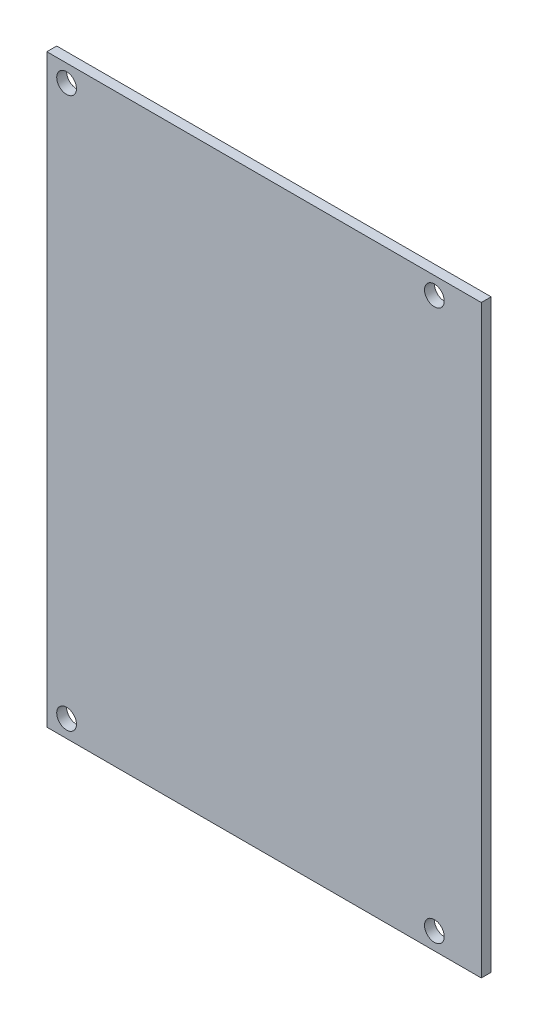
SolidWorks part; units mm, degrees
ref_plane "Plan de face" through (0, 0, 0) normal (0, 0, 1) x (1, 0, 0)
ref_plane "Plan de dessus" through (0, 0, 0) normal (0, 1, 0) x (1, 0, 0)
ref_plane "Plan de droite" through (0, 0, 0) normal (1, 0, 0) x (0, 0, -1)
sketch "Main-Sketch" plane through (0, 0, 0) normal (0, 0, 1) x (1, 0, 0)
  line L1 (-44, -59.25) -> (44, -59.25)
  line L2 (-44, -59.25) -> (-44, 59.25)
  line L3 (-44, 59.25) -> (44, 59.25)
  line L4 (44, -59.25) -> (44, 59.25)
  point P5 (-21.6785, -5.2182)
  point P6 (-44, 0)
  point P8 (0, -59.25)
  dimension "D1" = 88
  dimension "D2" = 118.5
extrude "Main-Extrusion" add sketch "Main-Sketch" along normal blind 2
sketch "Fix-Sketch" plane through (0, 0, 2) normal (0, 0, 1) x (1, 0, 0)
  line L0 (44, 59.25) -> (-44, 59.25) construction
  line L2 (-44, 59.25) -> (-44, -59.25) construction
  line L3 (-44, -59.25) -> (44, -59.25) construction
  circle A0 centre (-40, 55.75) radius 2
  circle A1 centre (-40, -55.75) radius 2
  circle A2 centre (34.5, -55.75) radius 2
  circle A3 centre (34.5, 55.75) radius 2
  dimension "D1" = 3.5
  dimension "D2" = 4
  dimension "D3" = 111.5
  dimension "D4" = 4
  dimension "D5" = 3.5
  dimension "D6" = 74.5
extrude "Fix-Hole" cut sketch "Fix-Sketch" against normal through all
